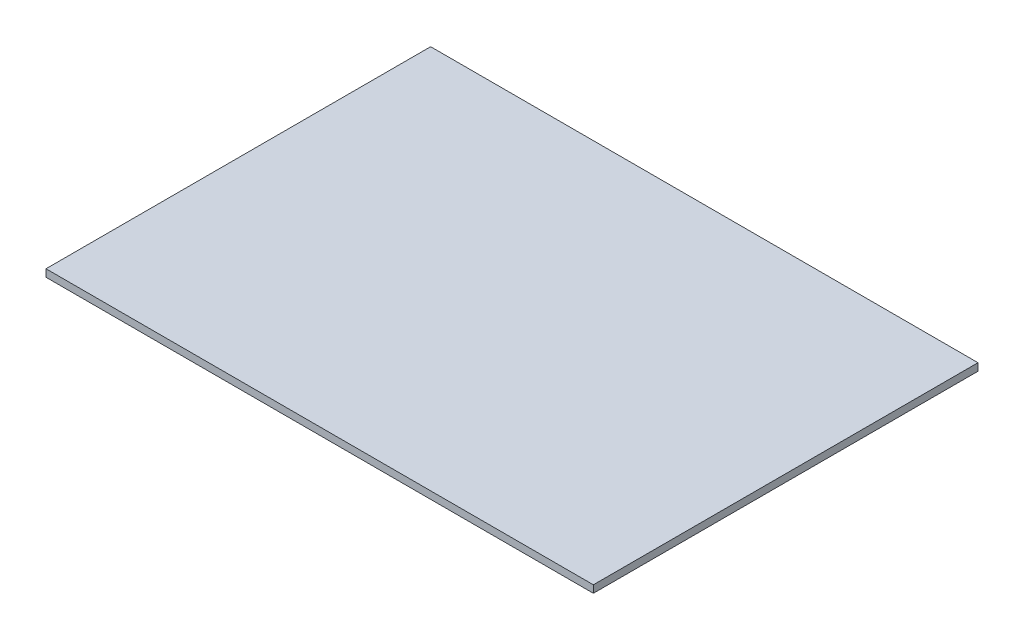
SolidWorks part; units mm, degrees
ref_plane "Front Plane" through (0, 0, 0) normal (0, 0, 1) x (1, 0, 0)
ref_plane "Top Plane" through (0, 0, 0) normal (0, 1, 0) x (1, 0, 0)
ref_plane "Right Plane" through (0, 0, 0) normal (1, 0, 0) x (0, 0, -1)
sketch "Sketch1" plane through (0, 0, 0) normal (0, 1, 0) x (1, 0, 0)
  line L1 (-185, 130) -> (185, 130)
  line L2 (-185, 130) -> (-185, -130)
  line L3 (-185, -130) -> (185, -130)
  line L4 (185, 130) -> (185, -130)
  line L5 (-185, 130) -> (185, -130) construction
  line L6 (-185, -130) -> (185, 130) construction
  point P0 (0, 0)
  dimension "D1" = 370
  dimension "D2" = 260
extrude "Boss-Extrude1" add sketch "Sketch1" along normal blind 5
